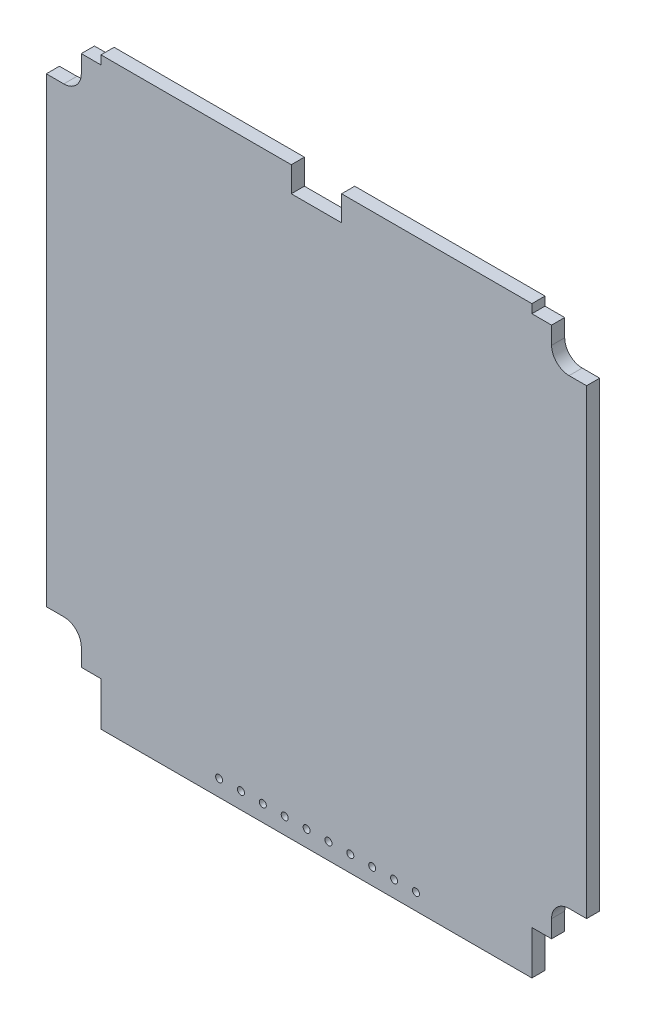
SolidWorks part; units mm, degrees
ref_plane "Front" through (0, 0, 0) normal (0, 0, 1) x (1, 0, 0)
ref_plane "Top" through (0, 0, 0) normal (0, 1, 0) x (1, 0, 0)
ref_plane "Right" through (0, 0, 0) normal (1, 0, 0) x (0, 0, -1)
sketch "Sketch1" plane through (0, 0, 0) normal (0, 0, 1) x (1, 0, 0)
  line L0 (-31.369, 0) -> (31.369, 0) construction
  line L1 (-31.369, 33.909) -> (31.369, 33.909)
  line L2 (-31.369, 33.909) -> (-31.369, -33.909)
  line L3 (-31.369, -33.909) -> (31.369, -33.909)
  line L4 (31.369, 33.909) -> (31.369, -33.909)
  point P6 (0, 0)
  dimension "D1" = 62.738
  dimension "D2" = 67.818
extrude "PCB" add sketch "Sketch1" along normal blind 1.524
sketch "Sketch2" plane through (0, 0, 1.524) normal (0, 0, 1) x (1, 0, 0)
  line L0 (-31.369, 28.829) -> (-29.337, 28.829)
  line L1 (-31.369, 33.909) -> (-31.369, -33.909) construction
  line L2 (-27.305, 30.861) -> (-27.305, 32.893)
  line L3 (-27.305, 32.893) -> (-25.019, 32.893)
  line L4 (-25.019, 32.893) -> (-25.019, 40.259)
  line L5 (-25.019, 40.259) -> (-31.369, 40.259)
  line L6 (-31.369, 40.259) -> (-31.369, 28.829)
  line L7 (31.369, 33.909) -> (-31.369, 33.909) construction
  arc A0 (-29.337, 28.829) -> (-27.305, 30.861) centre (-29.337, 30.861) ccw
  dimension "D3" = 2.032
  dimension "D1" = 1.016
  dimension "D2" = 4.064
  dimension "D4" = 6.35
  dimension "D5" = 6.35
extrude "cut1" cut sketch "Sketch2" against normal through all
mirror "Mirror1" about plane through (0, 0, 0) normal (1, 0, 0) of "cut1"
ref_plane "Plane1" through (0, 2.032, 0) normal (0, -1, 0) x (1, 0, 0)
mirror "Mirror3" about plane through (0, 2.032, 0) normal (0, -1, 0) of "cut1", "Mirror1"
sketch "Sketch4" plane through (0, 0, 0) normal (0, 0, -1) x (-1, 0, 0)
  line L0 (-25.019, 33.909) -> (25.019, 33.909) construction
  line L1 (-2.921, 33.909) -> (2.921, 33.909)
  line L2 (-2.921, 33.909) -> (-2.921, 30.988)
  line L3 (-2.921, 30.988) -> (2.921, 30.988)
  line L4 (2.921, 33.909) -> (2.921, 30.988)
  line L5 (0, 0) -> (0, 30.988) construction
  dimension "D1" = 5.842
  dimension "D2" = 2.921
extrude "cutout" cut sketch "Sketch4" against normal blind 1.524
sketch "Sketch3" plane through (0, 0, 1.524) normal (0, 0, 1) x (1, 0, 0)
  line L0 (-25.019, -33.909) -> (25.019, -33.909) construction
  line L1 (-25.019, -28.829) -> (-25.019, -33.909) construction
  line L2 (-11.303, -32.004) -> (-8.763, -32.004) construction
  circle A0 centre (-11.303, -32.004) radius 0.4064
  circle A1 centre (-8.763, -32.004) radius 0.4064
  circle A2 centre (-6.223, -32.004) radius 0.4064
  circle A3 centre (-3.683, -32.004) radius 0.4064
  circle A4 centre (-1.143, -32.004) radius 0.4064
  circle A5 centre (1.397, -32.004) radius 0.4064
  circle A6 centre (3.937, -32.004) radius 0.4064
  circle A7 centre (6.477, -32.004) radius 0.4064
  circle A8 centre (9.017, -32.004) radius 0.4064
  circle A9 centre (11.557, -32.004) radius 0.4064
  dimension "D3" = 0.8128
  dimension "D1" = 1.905
  dimension "D2" = 13.716
  dimension "D4" = 2.54
extrude "holes" cut sketch "Sketch3" against normal through all
sketch "Sketch5" plane through (0, 0, 0) normal (0, 0, -1) x (-1, 0, 0)
  line L0 (-11.557, -32.639) -> (-11.557, -31.369) construction
  line L1 (-12.192, -32.639) -> (-12.192, -31.369)
  line L2 (-10.922, -32.639) -> (-10.922, -31.369)
  arc A0 (-12.192, -32.639) -> (-10.922, -32.639) centre (-11.557, -32.639) ccw
  arc A1 (-10.922, -31.369) -> (-12.192, -31.369) centre (-11.557, -31.369) ccw
  point P3 (-11.557, -32.004)
  dimension "D2" = 1.27
  dimension "D1" = 1.27
extrude "solder pad" add sketch "Sketch5" along normal blind 0.0254
pattern_linear "LPattern1" count 10 spacing 2.54 along (-1, 0, 0) of "solder pad"
